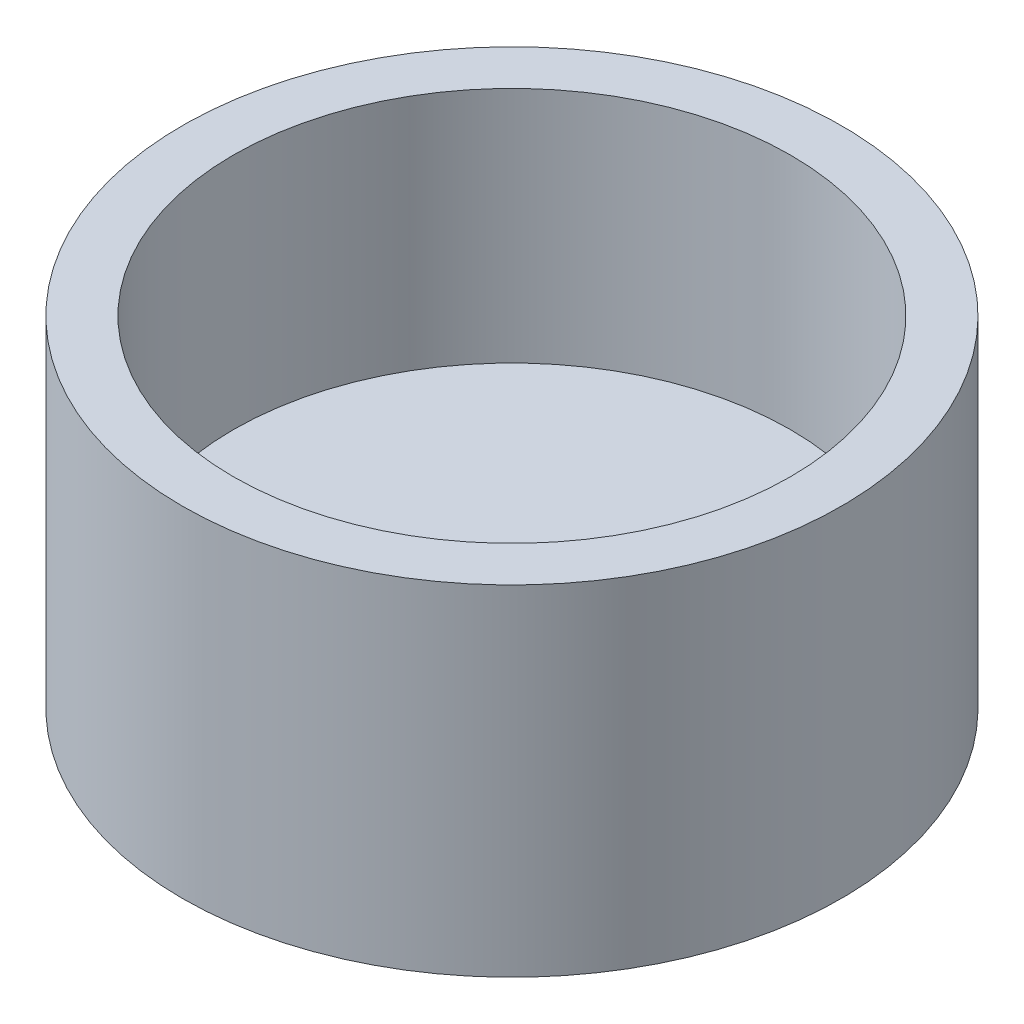
SolidWorks part; units mm, degrees
ref_plane "Front Plane" through (0, 0, 0) normal (0, 0, 1) x (1, 0, 0)
ref_plane "Top Plane" through (0, 0, 0) normal (0, 1, 0) x (1, 0, 0)
ref_plane "Right Plane" through (0, 0, 0) normal (1, 0, 0) x (0, 0, -1)
sketch "Sketch1" plane through (0, 0, 0) normal (0, 1, 0) x (1, 0, 0)
  circle A0 centre (0, 0) radius 4.85
extrude "Boss-Extrude1" add sketch "Sketch1" along normal blind 4 and the other way blind 1
sketch "Sketch2" plane through (0, 4, 0) normal (0, 1, 0) x (1, 0, 0)
  circle A0 centre (0, 0) radius 4.1
extrude "Cut-Extrude1" cut sketch "Sketch2" against normal blind 3.5
